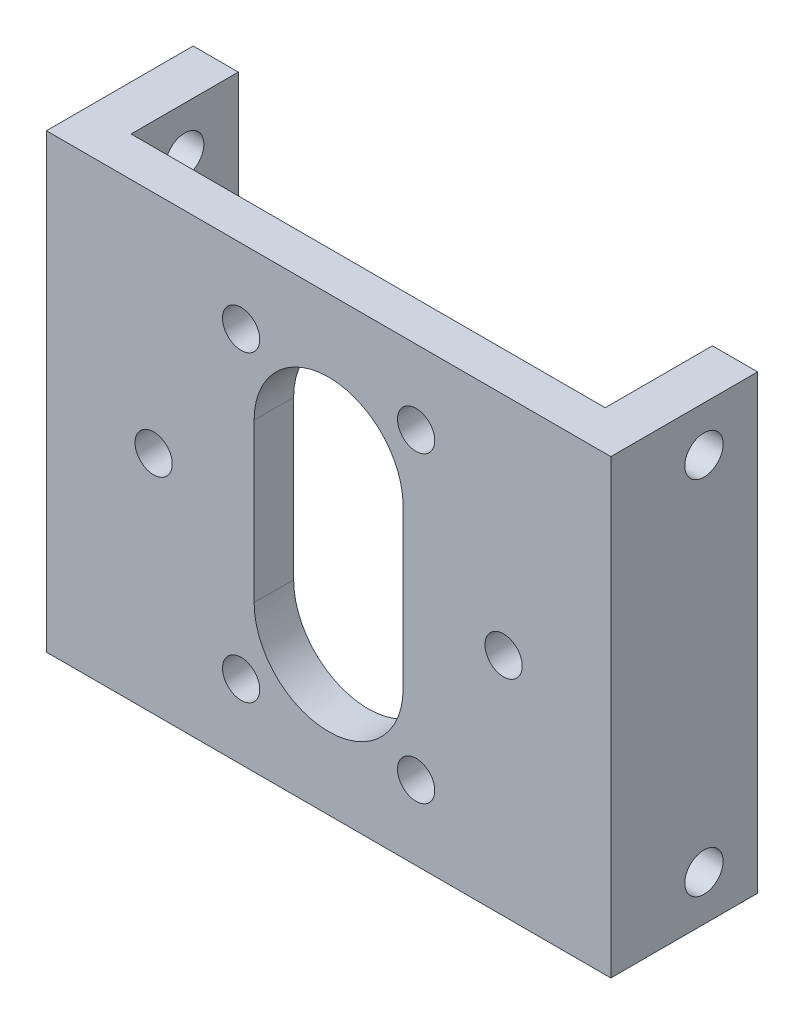
SolidWorks part; units mm, degrees
ref_plane "前视基准面" through (0, 0, 0) normal (0, 0, 1) x (1, 0, 0)
ref_plane "上视基准面" through (0, 0, 0) normal (0, 1, 0) x (1, 0, 0)
ref_plane "右视基准面" through (0, 0, 0) normal (1, 0, 0) x (0, 0, -1)
sketch "草图1" plane through (0, 0, 0) normal (0, 0, 1) x (1, 0, 0)
  line L0 (-25, 20) -> (-25, -20)
  line L1 (-25, 20) -> (25, 20)
  line L2 (25, 20) -> (25, -20)
  line L3 (25, -20) -> (-25, -20)
  line L4 (0, 0) -> (0, -20) construction
  line L5 (0, 0) -> (25, 0) construction
  dimension "D1" = 50
  dimension "D2" = 40
extrude "凸台-拉伸1" add sketch "草图1" along normal blind 5
sketch "草图2" plane through (0, 0, 0) normal (0, 0, -1) x (-1, 0, 0)
  line L0 (-19, -20) -> (-19, 20)
  line L1 (25, -20) -> (-25, -20) construction
  line L2 (-25, 20) -> (25, 20) construction
  line L3 (-19, 20) -> (-25, 20)
  line L4 (-25, 20) -> (-25, -20)
  line L5 (-25, -20) -> (-25, 20) construction
  line L6 (-25, -20) -> (-19, -20)
  line L7 (0, 20) -> (0, -20) construction
  line L8 (25, -20) -> (19, -20)
  line L9 (25, 20) -> (25, -20)
  line L10 (19, 20) -> (25, 20)
  line L11 (19, -20) -> (19, 20)
  dimension "D1" = 6
extrude "凸台-拉伸2" add sketch "草图2" along normal blind 8
sketch "草图3" plane through (0, 0, 0) normal (0, 0, -1) x (-1, 0, 0)
  line L0 (-15.5, 0) -> (15.5, 0) construction
  line L1 (0, 7) -> (0, -7) construction
  line L2 (-6.6, 7) -> (-6.6, -7)
  line L3 (6.6, 7) -> (6.6, -7)
  circle A0 centre (0, 0) radius 15.5 construction
  circle A1 centre (-15.5, 0) radius 1.65
  circle A2 centre (-7.75, 13.4234) radius 1.65
  circle A3 centre (7.75, 13.4234) radius 1.65
  circle A4 centre (15.5, 0) radius 1.65
  circle A5 centre (7.75, -13.4234) radius 1.65
  circle A6 centre (-7.75, -13.4234) radius 1.65
  arc A7 (-6.6, -7) -> (6.6, -7) centre (0, -7) ccw
  arc A8 (6.6, 7) -> (-6.6, 7) centre (0, 7) ccw
  point P18 (0, 0)
  dimension "D1" = 31
  dimension "D2" = 3.3
  dimension "D4" = 13.2
  dimension "D5" = 14
  dimension "D3" = 6
extrude "切除-拉伸1" cut sketch "草图3" against normal through all
sketch "草图4" plane through (0, 0, 0) normal (0, 0, -1) x (-1, 0, 0)
  line L0 (19, -20) -> (-19, -20) construction
  line L1 (19, 20) -> (19, -20) construction
  line L2 (-19, -20) -> (-19, 20) construction
  line L3 (-19, 20) -> (19, 20) construction
  line L4 (19, -20) -> (-19, -20)
  line L5 (19, 20) -> (19, -20)
  line L6 (-19, -20) -> (-19, 20)
  line L7 (-19, 20) -> (19, 20)
extrude "切除-拉伸2" cut sketch "草图4" against normal blind 1.5
sketch "草图6" plane through (-19, 0, 0) normal (1, 0, 0) x (0, 0, -1)
  line L0 (-1.5, 20) -> (-1.5, -20) construction
  line L1 (-1.5, -20) -> (8, -20) construction
  line L2 (8, -20) -> (8, 20) construction
  line L3 (8, 20) -> (-1.5, 20) construction
  line L4 (3.25, 20) -> (3.25, -20) construction
  line L5 (-1.5, 0) -> (8, 0) construction
  circle A0 centre (3.25, 16) radius 1.7
  circle A1 centre (3.25, -16) radius 1.7
  dimension "D1" = 3.4
  dimension "D2" = 16
extrude "切除-拉伸3" cut sketch "草图6" against normal through all both and the other way through all
sketch "草图7" plane through (0, -20, 0) normal (0, -1, 0) x (1, 0, 0)
  line L0 (21, -8) -> (21, 1.5)
  line L1 (25, -8) -> (19, -8) construction
  line L2 (21, 1.5) -> (-21, 1.5)
  line L3 (-21, 1.5) -> (-21, -8)
  line L4 (-19, -8) -> (-25, -8) construction
  line L5 (-21, -8) -> (21, -8)
  line L6 (25, 5) -> (25, -8) construction
  line L7 (-25, 5) -> (-25, -8) construction
  line L8 (19, 1.5) -> (-19, 1.5) construction
  point P12 (-21, 3.8335)
  dimension "D1" = 4
  dimension "D2" = 4
extrude "切除-拉伸4" cut sketch "草图7" against normal through all
